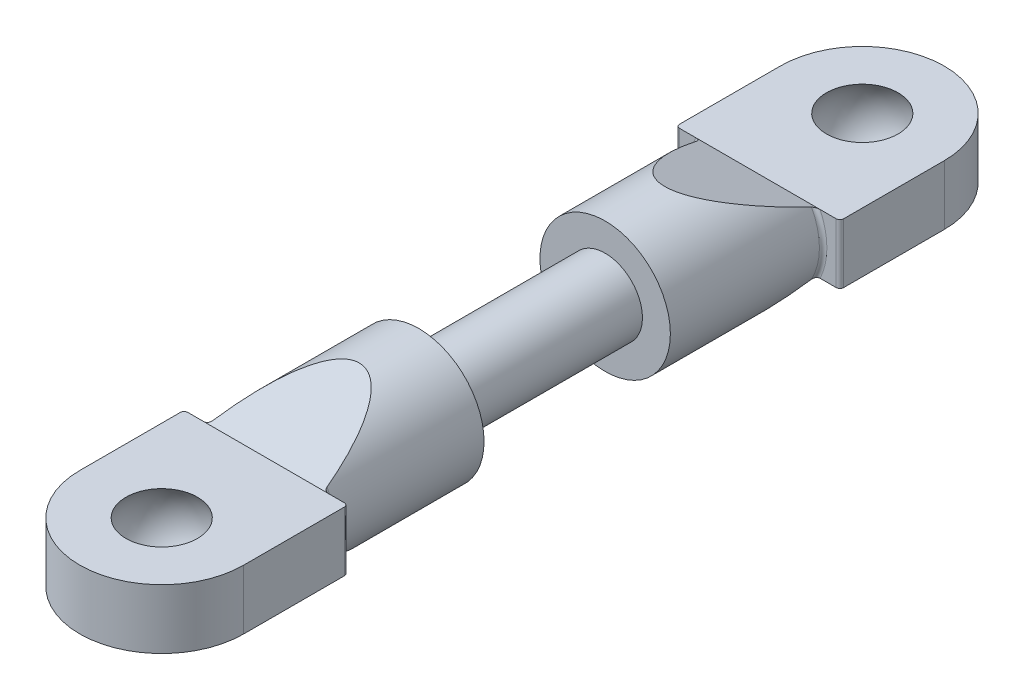
SolidWorks part; units mm, degrees
ref_plane "Front Plane" through (0, 0, 0) normal (0, 0, 1) x (1, 0, 0)
ref_plane "Top Plane" through (0, 0, 0) normal (0, 1, 0) x (1, 0, 0)
ref_plane "Right Plane" through (0, 0, 0) normal (1, 0, 0) x (0, 0, -1)
sketch "Sketch1" plane through (0, 0, 0) normal (0, 0, 1) x (1, 0, 0)
  circle A0 centre (0, 0) radius 2
  dimension "D1" = 4
extrude "Screw Section" add sketch "Sketch1" along normal blind 5 contours A0
sketch "Sketch2" plane through (0, 0, 5) normal (0, 0, 1) x (1, 0, 0)
  circle A0 centre (0, 0) radius 3.5
  dimension "D1" = 7
extrude "Bar Section" add sketch "Sketch2" along normal blind 8.2
sketch "Sketch3" plane through (0, 0, 0) normal (0, 1, 0) x (1, 0, 0)
  line L0 (4.4, -13.2) -> (-4.4, -13.2)
  line L1 (-4.4, -13.2) -> (-4.4, -18.8)
  line L2 (4.4, -13.2) -> (4.4, -18.8)
  line L3 (-3.5, -13.2) -> (3.5, -13.2) construction
  arc A0 (-4.4, -18.8) -> (4.4, -18.8) centre (0, -18.8) ccw
  point P4 (0, -23.2)
  dimension "D1" = 4.4
  dimension "D2" = 8.8
  dimension "D3" = 10
extrude "Mount Section" add sketch "Sketch3" along normal mid plane 3.2
sketch "Sketch4" plane through (0, 0, 0) normal (1, 0, 0) x (0, 0, -1)
  line L0 (-8.2, -3.5) -> (-13.2, -1.6)
  line L1 (-13.2, -3.5) -> (-5, -3.5) construction
  line L2 (-13.2, -1.6) -> (-13.2, -3.5)
  line L3 (-13.2, -1.6) -> (-13.2, -3.5) construction
  line L4 (-13.2, -3.5) -> (-8.2, -3.5)
  line L5 (-8.2, 3.5) -> (-13.2, 1.6)
  line L6 (-13.2, 3.5) -> (-13.2, 1.6) construction
  line L7 (-13.2, 3.5) -> (-8.2, 3.5)
  line L9 (-13.2, 1.6) -> (-13.2, 3.5)
  dimension "D1" = 5
  dimension "D2" = 1.9
extrude "Bar Taper" cut sketch "Sketch4" against normal through all both and the other way through all
fillet "Mount Fillet" radius 0.2 4 edges at (-4.4, 0, 13.2) (3.5, 0, 13.2) (-3.5, 0, 13.2) (4.4, 0, 13.2)
sketch "Sketch6" plane through (0, 0, 0) normal (1, 0, 0) x (0, 0, -1)
  line L0 (-18.8, 1.6) -> (-18.8, -1.6) construction
  line L1 (-23.2, -1.6) -> (-18.8, -1.6) construction
  line L2 (-18.8, 1.6) -> (-23.2, 1.6) construction
  line L4 (-20.7209, -1.6) -> (-18.8, -1.6)
  line L5 (-18.8, -1.6) -> (-18.8, 1.6)
  line L6 (-18.8, 1.6) -> (-20.7209, 1.6)
  arc A0 (-20.7209, -1.6) -> (-20.7209, 1.6) centre (-18.8, 0) cw
  dimension "D1" = 2.5
revolve "Ball Hole" cut sketch "Sketch6" angle 360 about L5
mirror "Mirror" of "Ball Hole", "Bar Section", "Bar Taper", "Mount Section", "Mount Fillet", "Screw Section"
ref_point "Point1"
ref_point "Point2"
